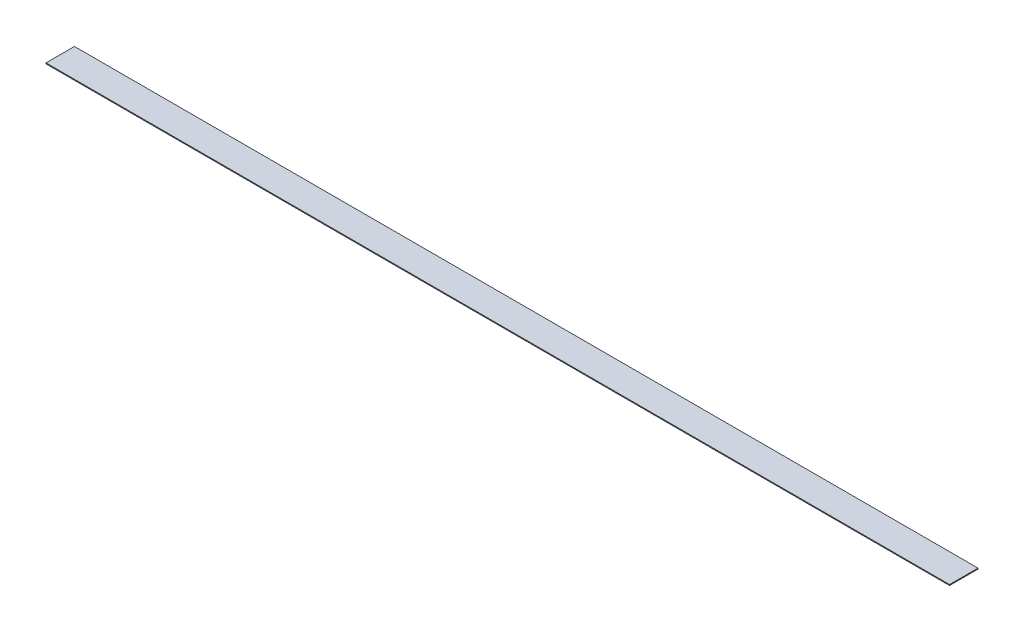
SolidWorks part; units mm, degrees
ref_plane "Front Plane" through (0, 0, 0) normal (0, 0, 1) x (1, 0, 0)
ref_plane "Top Plane" through (0, 0, 0) normal (0, 1, 0) x (1, 0, 0)
ref_plane "Right Plane" through (0, 0, 0) normal (1, 0, 0) x (0, 0, -1)
sketch "Sketch1" plane through (0, 0, 0) normal (0, 1, 0) x (1, 0, 0)
  line L1 (0, 0) -> (1612.9, 0)
  line L2 (0, 0) -> (0, 50.8)
  line L3 (0, 50.8) -> (1612.9, 50.8)
  line L4 (1612.9, 0) -> (1612.9, 50.8)
  dimension "D1" = 50.8
  dimension "D2" = 1612.9
extrude "Boss-Extrude1" add sketch "Sketch1" along normal blind 1.5875
